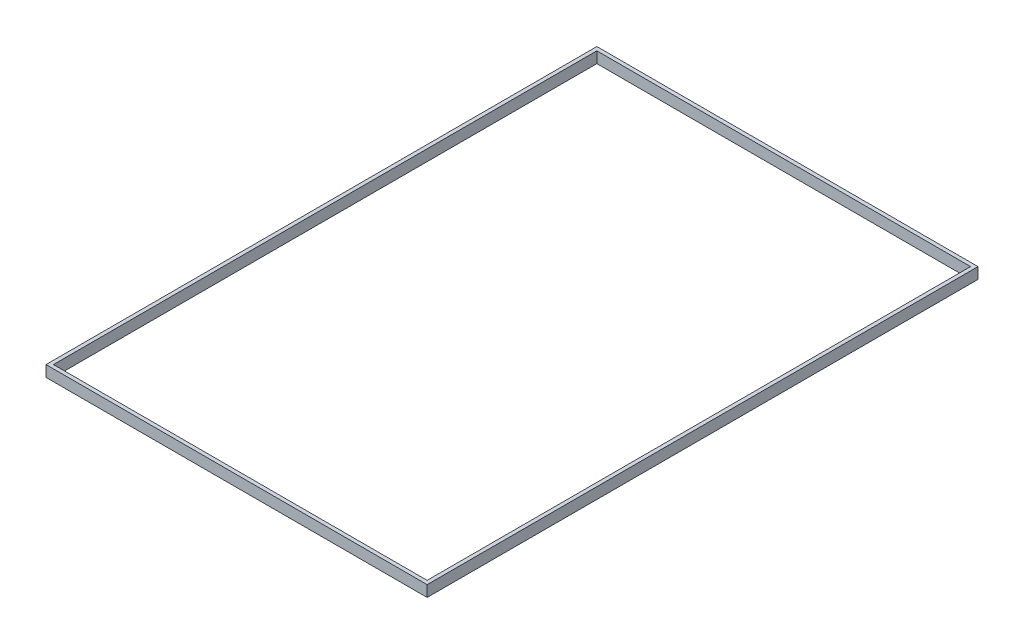
SolidWorks part; units mm, degrees
ref_plane "Front Plane" through (0, 0, 0) normal (0, 0, 1) x (1, 0, 0)
ref_plane "Top Plane" through (0, 0, 0) normal (0, 1, 0) x (1, 0, 0)
ref_plane "Right Plane" through (0, 0, 0) normal (1, 0, 0) x (0, 0, -1)
sketch "Sketch1" plane through (0, 0, 0) normal (0, 1, 0) x (1, 0, 0)
  line L0 (0, 148.5) -> (1, 148.5) construction
  line L1 (0, 0) -> (102.75, 0)
  line L2 (0, 0) -> (0, 148.5)
  line L3 (0, 148.5) -> (102.75, 148.5)
  line L4 (102.75, 0) -> (102.75, 148.5)
  line L5 (1, 148.5) -> (1, 147.5) construction
  line L6 (1, 147.5) -> (101.75, 147.5)
  line L7 (101.75, 147.5) -> (101.75, 1)
  line L8 (101.75, 1) -> (1, 1)
  line L9 (1, 1) -> (1, 147.5)
extrude "Boss-Extrude1" add sketch "Sketch1" along normal blind 3
